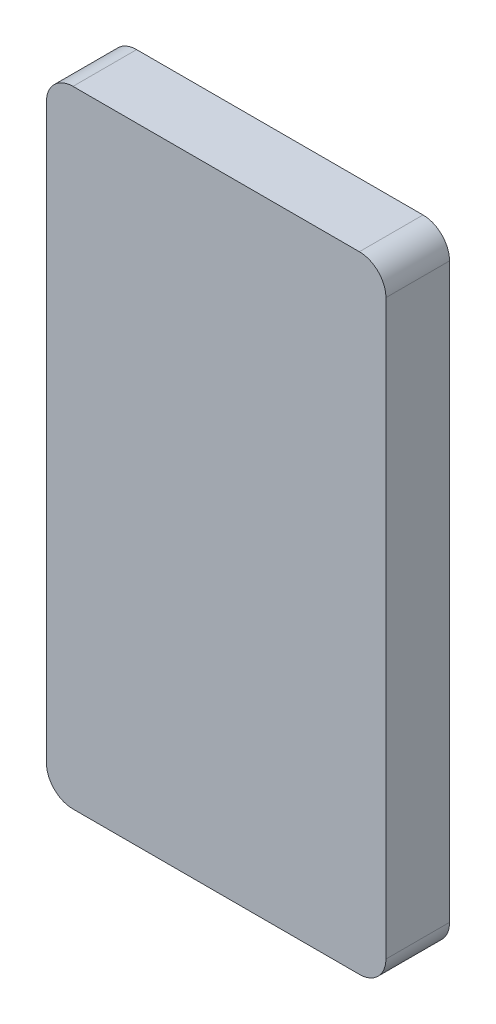
SolidWorks part; units mm, degrees
ref_plane "Ön Düzlem" through (0, 0, 0) normal (0, 0, 1) x (1, 0, 0)
ref_plane "Üst Düzlem" through (0, 0, 0) normal (0, 1, 0) x (1, 0, 0)
ref_plane "Sağ Düzlem" through (0, 0, 0) normal (1, 0, 0) x (0, 0, -1)
sketch "Sketch1" plane through (0, 0, 0) normal (0, 0, 1) x (1, 0, 0)
  line L1 (5, 0) -> (59, 0)
  line L2 (0, 5) -> (0, 113)
  line L3 (5, 118) -> (59, 118)
  line L4 (64, 5) -> (64, 113)
  arc A0 (5, 0) -> (0, 5) centre (5, 5) cw
  arc A1 (59, 0) -> (64, 5) centre (59, 5) ccw
  arc A2 (59, 118) -> (64, 113) centre (59, 113) cw
  arc A3 (0, 113) -> (5, 118) centre (5, 113) cw
  point P7 (0, 0)
  point P12 (64, 118)
  point P15 (0, 118)
  dimension "D3" = 5
  dimension "D1" = 118
  dimension "D2" = 64
extrude "Boss-Extrude1" add sketch "Sketch1" against normal blind 12
sketch "Sketch2" plane through (0, 0, 0) normal (1, 0, 0) x (0, 0, -1)
  line L0 (6, 28.85) -> (6, 36.15)
  line L2 (12, 0) -> (0, 0) construction
  line L3 (7.4, 28.85) -> (7.4, 36.15)
  line L4 (4.6, 28.85) -> (4.6, 36.15)
  line L5 (4.6, 36.15) -> (7.4, 36.15)
  line L6 (7.4, 28.85) -> (4.6, 28.85)
  point P2 (6, 0)
  point P6 (6, 32.5)
  dimension "D1" = 7.3
  dimension "D2" = 32.5
  dimension "D3" = 1.4
  dimension "D4" = 1.4
extrude "Cut-Extrude1" cut sketch "Sketch2" along normal blind 10 contours L3 L5 L4 L6
